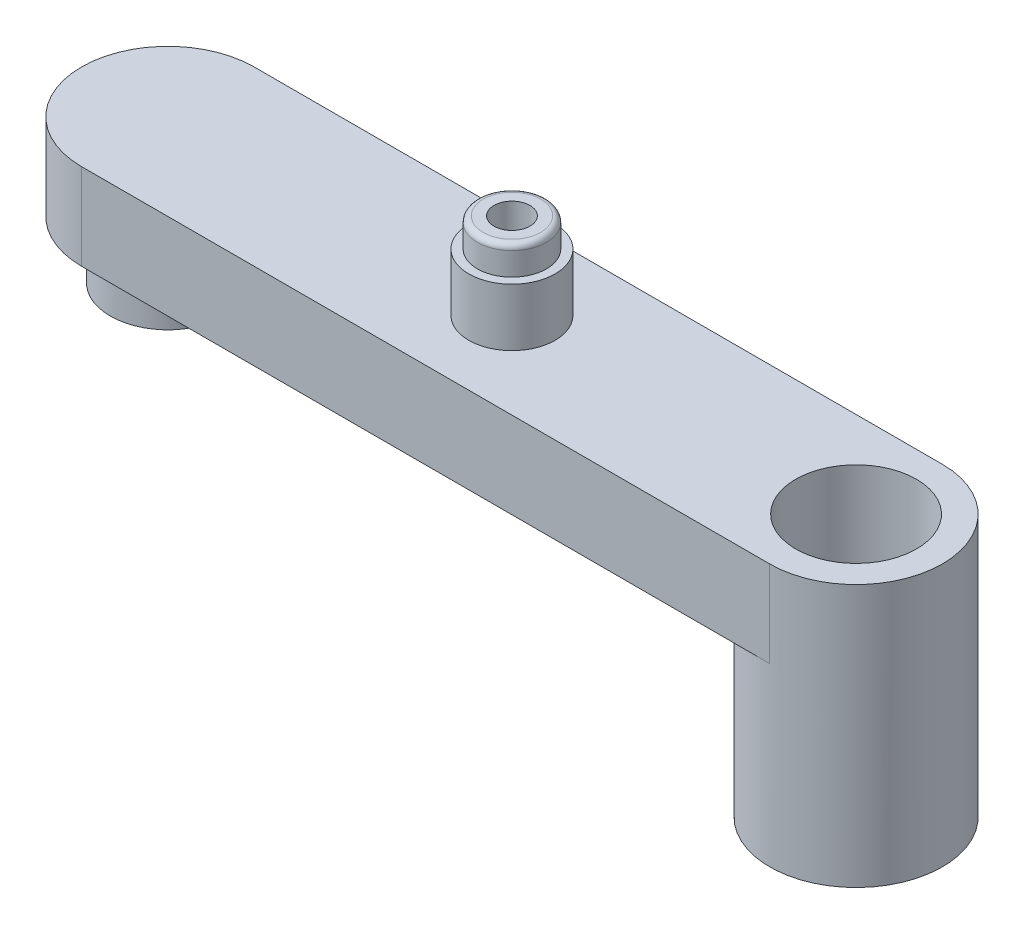
SolidWorks part; units mm, degrees
ref_plane "Front" through (0, 0, 0) normal (0, 0, 1) x (1, 0, 0)
ref_plane "Top" through (0, 0, 0) normal (0, 1, 0) x (1, 0, 0)
ref_plane "Right" through (0, 0, 0) normal (1, 0, 0) x (0, 0, -1)
sketch "Sketch1" plane through (0, 0, 0) normal (0, 1, 0) x (1, 0, 0)
  line L3 (-11.96, 3) -> (11.96, 3)
  line L6 (-11.96, -3) -> (11.96, -3)
  arc A2 (-11.96, 3) -> (-11.96, -3) centre (-11.96, 0) ccw
  arc A3 (11.96, -3) -> (11.96, 3) centre (11.96, 0) ccw
extrude "Boss-Extrude1" add sketch "Sketch1" along normal blind 3
sketch "Sketch2" plane through (0, 0, 0) normal (0, -1, 0) x (1, 0, 0)
  circle A0 centre (-11.96, 0) radius 2
extrude "Boss-Extrude2" add sketch "Sketch2" along normal blind 2
sketch "Sketch3" plane through (0, -2, 0) normal (0, -1, 0) x (1, 0, 0)
  circle A0 centre (-11.96, 0) radius 1.1
extrude "Cut-Extrude1" cut sketch "Sketch3" against normal blind 3.5
sketch "Sketch4" plane through (0, 0, 0) normal (0, -1, 0) x (1, 0, 0)
  circle A1 centre (11.96, 0) radius 3
extrude "Boss-Extrude3" add sketch "Sketch4" along normal blind 6.12
sketch "Sketch5" plane through (0, -6.12, 0) normal (0, -1, 0) x (1, 0, 0)
  circle A3 centre (11.96, 0) radius 2.1
extrude "Cut-Extrude3" cut sketch "Sketch5" against normal blind 9.12
sketch "Sketch7" plane through (0, 3, 0) normal (0, 1, 0) x (1, 0, 0)
  circle A2 centre (0, 0) radius 1.5
extrude "Boss-Extrude4" add sketch "Sketch7" along normal blind 2
sketch "Sketch8" plane through (0, 5, 0) normal (0, 1, 0) x (1, 0, 0)
  circle A0 centre (0, 0) radius 1.2
extrude "Boss-Extrude5" add sketch "Sketch8" along normal blind 1
sketch "Sketch9" plane through (0, 6, 0) normal (0, 1, 0) x (1, 0, 0)
  circle A0 centre (0, 0) radius 0.625
extrude "Cut-Extrude6" cut sketch "Sketch9" against normal blind 3.5
fillet "Fillet2" radius 0.2 1 edges at (0, 6, 1.2)
